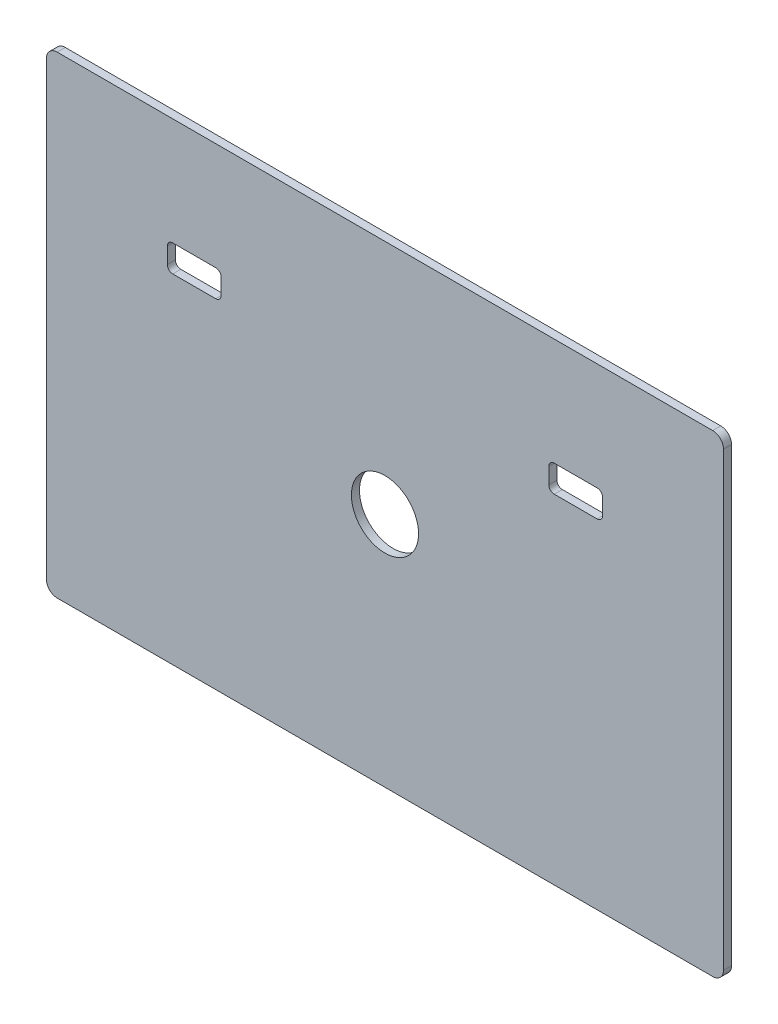
SolidWorks part; units mm, degrees
ref_plane "Front Plane" through (0, 0, 0) normal (0, 0, 1) x (1, 0, 0)
ref_plane "Top Plane" through (0, 0, 0) normal (0, 1, 0) x (1, 0, 0)
ref_plane "Right Plane" through (0, 0, 0) normal (1, 0, 0) x (0, 0, -1)
sketch "Sketch1" plane through (0, 0, 0) normal (0, 0, 1) x (1, 0, 0)
  line L1 (-126, 88) -> (126, 88)
  line L2 (-126, 88) -> (-126, -88)
  line L3 (-126, -88) -> (126, -88)
  line L4 (126, 88) -> (126, -88)
  line L5 (-126, 88) -> (126, -88) construction
  line L6 (-126, -88) -> (126, 88) construction
  point P0 (0, 0)
  dimension "D1" = 176
  dimension "D2" = 252
extrude "Boss-Extrude1" add sketch "Sketch1" along normal blind 3
sketch "Sketch2" plane through (0, 0, 3) normal (0, 0, 1) x (1, 0, 0)
  line L0 (0, 88) -> (0, -88) construction
  line L1 (126, 88) -> (-126, 88) construction
  line L2 (-126, -88) -> (126, -88) construction
  line L3 (-126, 88) -> (-126, -88) construction
  line L4 (-81, 48) -> (-61, 48)
  line L5 (-81, 48) -> (-81, 38)
  line L6 (-81, 38) -> (-61, 38)
  line L7 (-61, 48) -> (-61, 38)
  line L8 (126, -88) -> (126, 88) construction
  line L9 (81, 38) -> (61, 38)
  line L10 (81, 38) -> (81, 48)
  line L11 (81, 48) -> (61, 48)
  line L12 (61, 38) -> (61, 48)
  circle A0 centre (0, 0) radius 12.5
  dimension "D9" = 25
  dimension "D1" = 10
  dimension "D2" = 20
  dimension "D3" = 45
  dimension "D4" = 40
  dimension "D5" = 20
  dimension "D6" = 10
  dimension "D7" = 45
  dimension "D8" = 40
extrude "Cut-Extrude1" cut sketch "Sketch2" against normal through all
fillet "Fillet2" radius 2 8 edges at (61, 48, 1.5) (81, 48, 1.5) (81, 38, 1.5) (61, 38, 1.5) (-61, 38, 1.5) (-81, 38, 1.5) (-81, 48, 1.5) (-61, 48, 1.5)
fillet "Fillet3" radius 4 4 edges at (-126, -88, 1.5) (126, -88, 1.5) (126, 88, 1.5) (-126, 88, 1.5)
